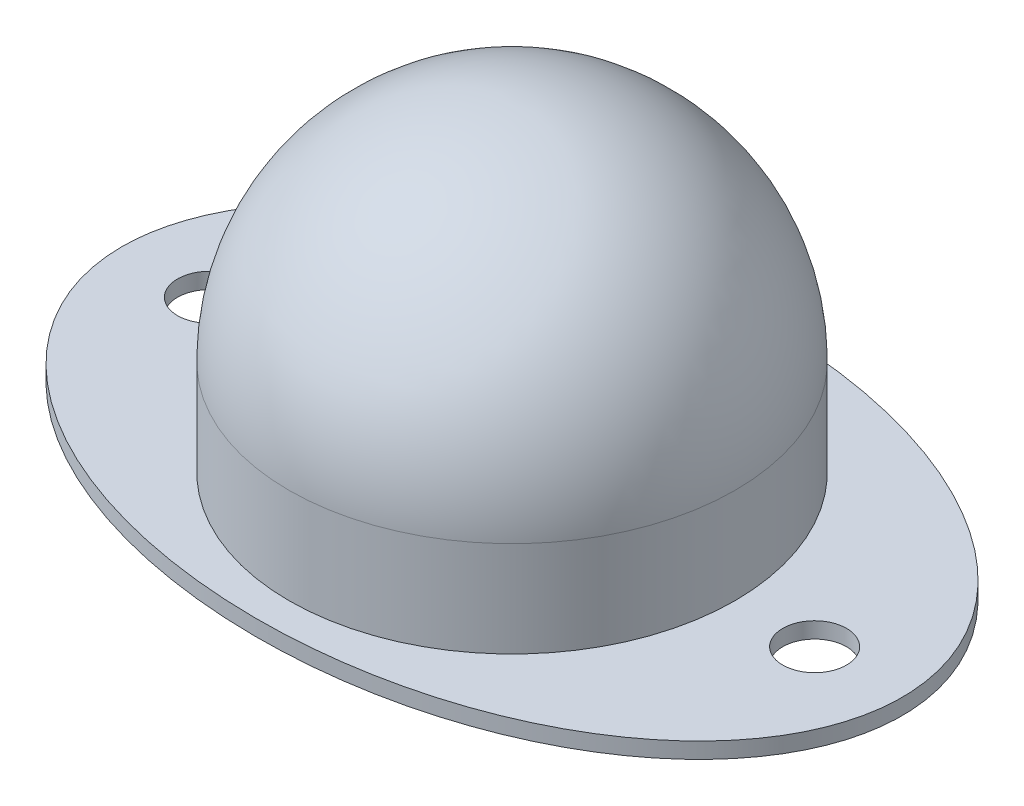
SolidWorks part; units mm, degrees
ref_plane "Front Plane" through (0, 0, 0) normal (0, 0, 1) x (1, 0, 0)
ref_plane "Top Plane" through (0, 0, 0) normal (0, 1, 0) x (1, 0, 0)
ref_plane "Right Plane" through (0, 0, 0) normal (1, 0, 0) x (0, 0, -1)
sketch "Sketch1" plane through (0, 0, 0) normal (0, 1, 0) x (1, 0, 0)
  ellipse E0 centre (0, 0) end of major axis (-24.5, 0) minor radius 16
  dimension "D1" = 49
  dimension "D2" = 32
extrude "Base" add sketch "Sketch1" along normal blind 1
sketch "Sketch2" plane through (0, 1, 0) normal (0, 1, 0) x (1, 0, 0)
  circle A0 centre (0, 0) radius 14
  dimension "D1" = 28
extrude "Suporte-esfera" add sketch "Sketch2" along normal blind 20
fillet "Fillet1" radius 14 1 edges at (0, 21, 14)
sketch "Sketch3" plane through (0, 1, 0) normal (0, 1, 0) x (1, 0, 0)
  line L0 (-24.5, 0) -> (24.5, 0) construction
  circle A0 centre (-19, 0) radius 2
  circle A1 centre (19, 0) radius 2
  ellipse E0 centre (0, 0) end of major axis (-24.5, 0) minor radius 16 construction
  dimension "D1" = 5.5
  dimension "D3" = 38
  dimension "D4" = 4
  dimension "D2" = 5.5
extrude "Furos-base" cut sketch "Sketch3" against normal through all
